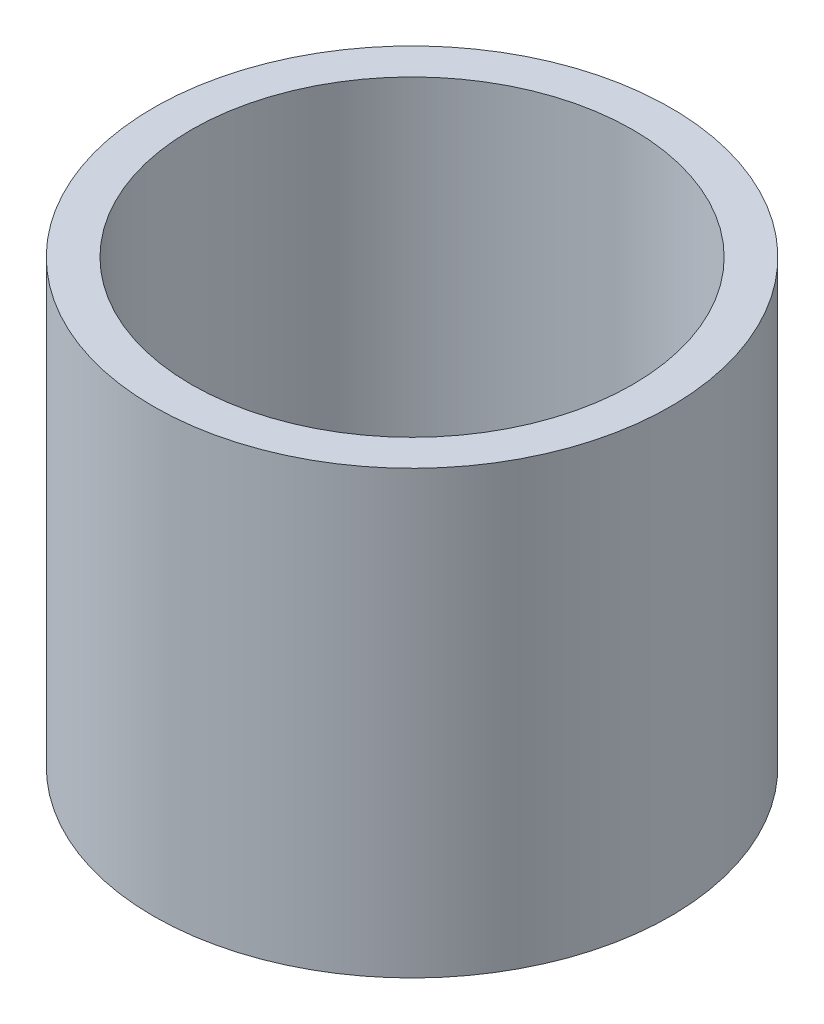
SolidWorks part; units mm, degrees
material "AISI 316 Annealed Stainless Steel Bar (SS)"
ref_plane "Front Plane" through (0, 0, 0) normal (0, 0, 1) x (1, 0, 0)
ref_plane "Top Plane" through (0, 0, 0) normal (0, 1, 0) x (1, 0, 0)
ref_plane "Right Plane" through (0, 0, 0) normal (1, 0, 0) x (0, 0, -1)
sketch "Sketch1" plane through (0, 0, 0) normal (0, 0, 1) x (1, 0, 0)
  line L0 (0, 0) -> (0, -7.683) construction
  line L1 (-6.35, 0) -> (-7.4422, 0)
  line L2 (-6.35, 0) -> (-6.35, -12.7)
  line L3 (-6.35, -12.7) -> (-7.4422, -12.7)
  line L4 (-7.4422, 0) -> (-7.4422, -12.7)
  dimension "D1" = 6.35
  dimension "D2" = 7.4422
  dimension "D3" = 12.7
revolve "Revolve1" add sketch "Sketch1" angle 360 about L0
